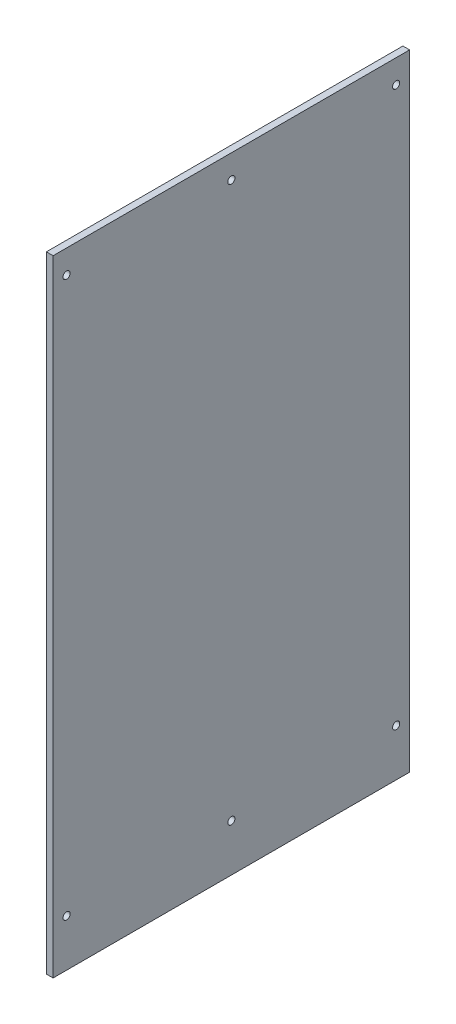
SolidWorks part; units mm, degrees
material "PC High Viscosity"
ref_plane "Front Plane" through (0, 0, 0) normal (0, 0, 1) x (1, 0, 0)
ref_plane "Top Plane" through (0, 0, 0) normal (0, 1, 0) x (1, 0, 0)
ref_plane "Right Plane" through (0, 0, 0) normal (1, 0, 0) x (0, 0, -1)
sketch "Sketch1" plane through (0, 0, 0) normal (1, 0, 0) x (0, 0, -1)
  line L1 (0, 0) -> (336.55, 0)
  line L2 (0, 0) -> (0, 590.55)
  line L3 (0, 590.55) -> (336.55, 590.55)
  line L4 (336.55, 0) -> (336.55, 590.55)
  dimension "D1" = 336.55
  dimension "D2" = 590.55
extrude "Boss-Extrude1" add sketch "Sketch1" along normal blind 6.35
sketch "Sketch2" plane through (6.35, 0, 0) normal (1, 0, 0) x (0, 0, -1)
  line L0 (336.55, 590.55) -> (0, 590.55) construction
  line L1 (336.55, 0) -> (336.55, 590.55) construction
  circle A0 centre (323.85, 568.325) radius 3.3782
  circle A1 centre (323.85, 44.45) radius 3.3782
  dimension "D1" = 6.7564
  dimension "D2" = 22.225
  dimension "D3" = 546.1
  dimension "D4" = 12.7
extrude "Cut-Extrude1" cut sketch "Sketch2" against normal blind 6.35
pattern_linear "LPattern1" count 3 spacing 155.575 along (0, 0, 1) of "Cut-Extrude1"
